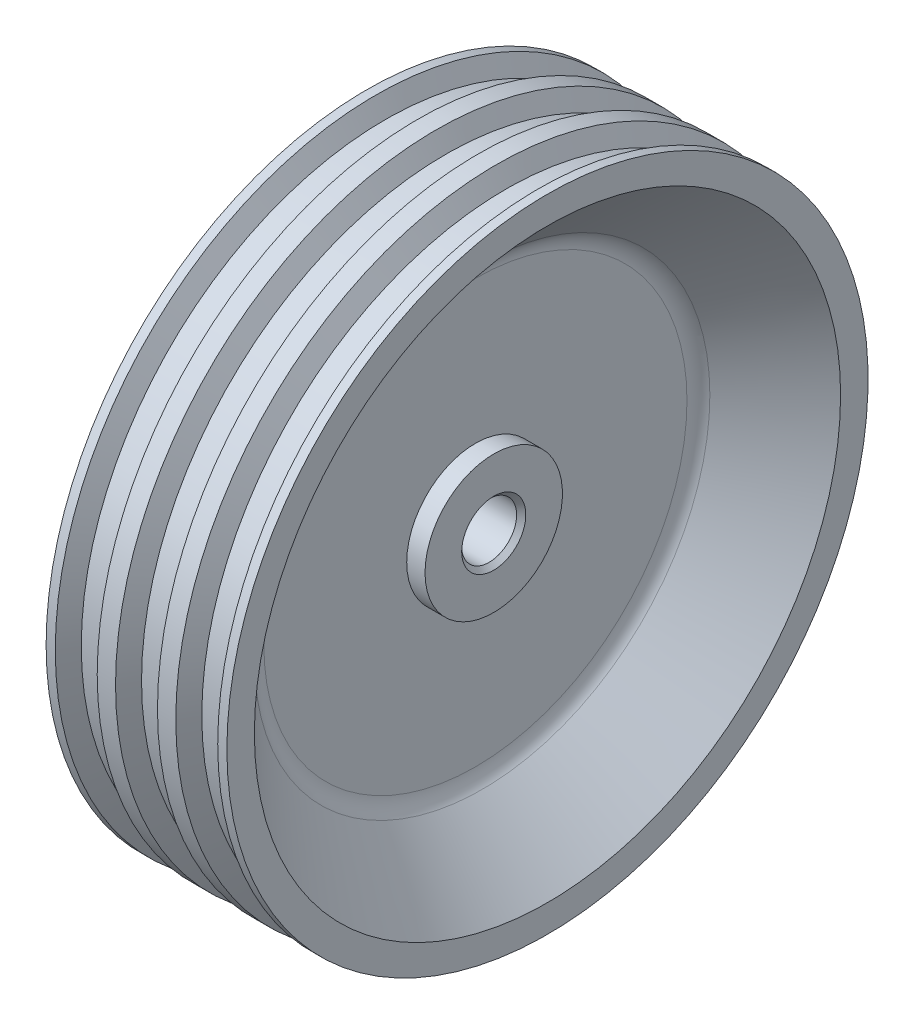
SolidWorks part; units mm, degrees
ref_plane "Płaszczyzna przednia" through (0, 0, 0) normal (0, 0, 1) x (1, 0, 0)
ref_plane "Płaszczyzna górna" through (0, 0, 0) normal (0, 1, 0) x (1, 0, 0)
ref_plane "Płaszczyzna prawa" through (0, 0, 0) normal (1, 0, 0) x (0, 0, -1)
sketch "Szkic2" plane through (0, 0, 0) normal (0, 1, 0) x (1, 0, 0)
  line L0 (-55, 0) -> (55, 0) construction
  line L1 (-8, 0) -> (-8, 15)
  line L2 (-8, 15) -> (-4, 15)
  line L3 (-4, 15) -> (-4, 48.2646)
  line L4 (-4, 48.2646) -> (-19.7354, 64)
  line L5 (-19.7354, 64) -> (-19.7354, 70)
  line L6 (-19.7354, 70) -> (-17.7354, 70)
  line L7 (-17.7354, 70) -> (-15.6569, 66.4)
  line L8 (-15.6569, 66.4) -> (-10.6569, 66.4)
  line L9 (-10.6569, 66.4) -> (-8.5785, 70)
  line L10 (-8.5785, 70) -> (-4.5785, 70)
  line L11 (-4.5785, 70) -> (-2.5, 66.4)
  line L12 (-2.5, 66.4) -> (2.5, 66.4)
  line L13 (0, -55) -> (0, 55) construction
  line L14 (4.5785, 70) -> (2.5, 66.4)
  line L15 (8.5785, 70) -> (4.5785, 70)
  line L16 (10.6569, 66.4) -> (8.5785, 70)
  line L17 (15.6569, 66.4) -> (10.6569, 66.4)
  line L18 (17.7354, 70) -> (15.6569, 66.4)
  line L19 (19.7354, 70) -> (17.7354, 70)
  line L20 (19.7354, 64) -> (19.7354, 70)
  line L21 (4, 48.2646) -> (19.7354, 64)
  line L22 (4, 15) -> (4, 48.2646)
  line L23 (8, 15) -> (4, 15)
  line L24 (8, 0) -> (8, 15)
  line L25 (-13.758, 0) -> (13.6025, 0) construction
  line L26 (-8, 0) -> (8, 0)
  point P17 (-18.7354, 70)
  point P20 (0, 66.4)
  dimension "D1" = 2.5
  dimension "D2" = 5
  dimension "D3" = 60
  dimension "D4" = 60
  dimension "D6" = 2
  dimension "D7" = 6
  dimension "D8" = 45
  dimension "D9" = 70
  dimension "D10" = 4
  dimension "D11" = 8
  dimension "D12" = 15
  dimension "D13" = 4
  dimension "D14" = 3.6
revolve "Obrót1" add sketch "Szkic2" angle 360 about L25
hole_wizard "Otwór Ø12.0 (12)1" positions "Szkic3" profile "Szkic4" hole size "Ø12.0" standard "ISO" end condition through all
sketch "Szkic3" plane through (8, 0, 0) normal (1, 0, 0) x (0, 0, -1)
  point P0 (0, 0)
sketch "Szkic4" plane through (8, 0, 0) normal (0, 1, 0) x (0, 0, -1)
  line L0 (0, 0) -> (0, 27.7354)
  line L1 (0, 27.7354) -> (6, 27.7354)
  line L2 (6, 27.7354) -> (6, 0)
  line L5 (6, 0) -> (0, 0)
  line L11 (0, -6.35) -> (0, 107.95) construction
  dimension "Średnica otworu na wylot" = 12
  dimension "Głębokość otworu na wylot" = 27.7354
fillet "Zaokrąglenie1" radius 5 1 edges at (4, 0, 48.2646)
fillet "Zaokrąglenie2" radius 5 1 edges at (-4, 0, 48.2646)
chamfer "Sfazowanie1" distance 1 angle 45 2 edges at (-8, 0, -6) (8, 0, -6)
